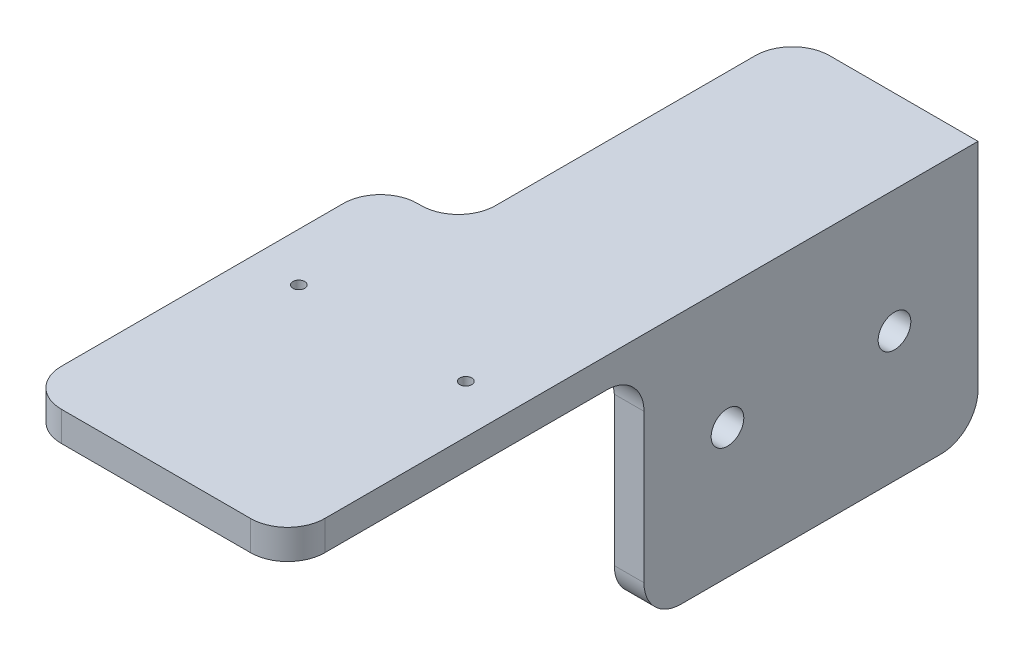
SolidWorks part; units mm, degrees
ref_plane "Front Plane" through (0, 0, 0) normal (0, 0, 1) x (1, 0, 0)
ref_plane "Top Plane" through (0, 0, 0) normal (0, 1, 0) x (1, 0, 0)
ref_plane "Right Plane" through (0, 0, 0) normal (1, 0, 0) x (0, 0, -1)
sketch "Sketch1" plane through (0, 0, 0) normal (0, 1, 0) x (1, 0, 0)
  line L0 (-35.5, 13) -> (35.5, 13) construction
  line L1 (-25.5, 48) -> (-24.5, 48)
  line L2 (-35.5, 38) -> (-35.5, -38)
  line L3 (-25.5, -48) -> (25.5, -48)
  line L4 (35.5, 48) -> (35.5, -38)
  line L5 (-35.5, 48) -> (35.5, -48) construction
  line L6 (-35.5, -48) -> (35.5, 48) construction
  line L8 (35.5, 48) -> (35.5, 138)
  line L9 (35.5, 138) -> (-4.5, 138)
  line L10 (-14.5, 58) -> (-14.5, 128)
  line L11 (-22.5, -48) -> (-22.5, 13) construction
  line L12 (22.5, -48) -> (22.5, 13) construction
  arc A0 (-24.5, 48) -> (-14.5, 58) centre (-24.5, 58) ccw
  arc A1 (-25.5, -48) -> (-35.5, -38) centre (-25.5, -38) cw
  arc A2 (35.5, -38) -> (25.5, -48) centre (25.5, -38) cw
  arc A3 (-35.5, 38) -> (-25.5, 48) centre (-25.5, 38) cw
  arc A4 (-4.5, 138) -> (-14.5, 128) centre (-4.5, 128) ccw
  circle A5 centre (-22.5, 13) radius 1.6
  circle A6 centre (22.5, 13) radius 1.6
  point P0 (0, 0)
  point P22 (-14.5, 138)
  dimension "D1" = 10
  dimension "D3" = 10
  dimension "D5" = 10
  dimension "D2" = 71
  dimension "D4" = 50
  dimension "D6" = 61
  dimension "D7" = 13
  dimension "D8" = 13
extrude "Boss-Extrude1" add sketch "Sketch1" along normal blind 8
sketch "Sketch2" plane through (0, 0, 0) normal (0, -1, 0) x (1, 0, 0)
  line L1 (35.5, -138) -> (27.5, -138)
  line L2 (35.5, -138) -> (35.5, -48)
  line L3 (35.5, -48) -> (27.5, -48)
  line L4 (27.5, -138) -> (27.5, -48)
  dimension "D1" = 90
  dimension "D2" = 8
extrude "Boss-Extrude2" add sketch "Sketch2" along normal blind 60
fillet "Fillet1" radius 10 1 edges at (31.5, -60, -138)
fillet "Fillet2" radius 10 1 edges at (31.5, -60, -48)
sketch "Sketch3" plane through (35.5, 0, 0) normal (1, 0, 0) x (0, 0, -1)
  line L0 (48, -25) -> (138, -25) construction
  line L1 (48, -50) -> (48, 0) construction
  line L2 (138, 8) -> (138, -50) construction
  line L3 (70.5, -60) -> (70.5, -25) construction
  line L4 (128, -60) -> (58, -60) construction
  line L5 (115.5, -60) -> (115.5, -25) construction
  circle A0 centre (70.5, -25) radius 4.4
  circle A1 centre (115.5, -25) radius 4.4
  dimension "D1" = 22.5
  dimension "D2" = 22.5
extrude "Cut-Extrude1" cut sketch "Sketch3" against normal up to surface (8 mm away) up to face at (27.5, -37.357, -93)
fillet "Fillet3" radius 10 1 edges at (27.5, 0, -93)
fillet "Fillet4" radius 10 2 edges at (26.5, 0, -48) (24.5711, -2.9289, -48)
